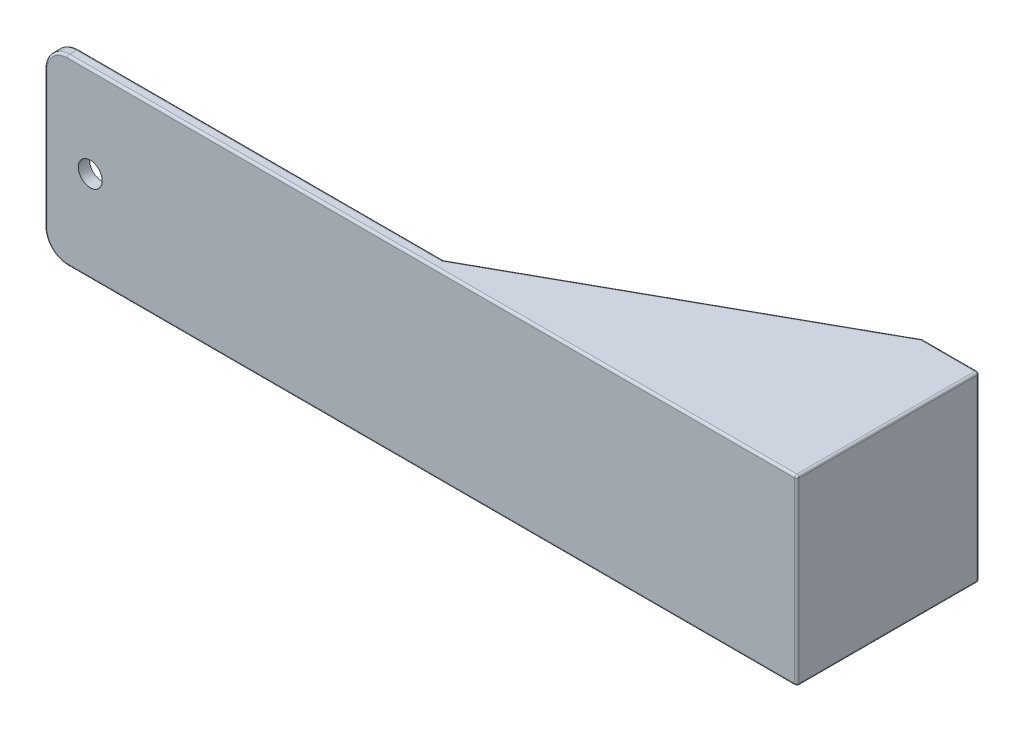
SolidWorks part; units mm, degrees
ref_plane "前视基准面" through (0, 0, 0) normal (0, 0, 1) x (1, 0, 0)
ref_plane "上视基准面" through (0, 0, 0) normal (0, 1, 0) x (1, 0, 0)
ref_plane "右视基准面" through (0, 0, 0) normal (1, 0, 0) x (0, 0, -1)
sketch "草图1" plane through (0, 0, 0) normal (0, 0, 1) x (1, 0, 0)
  line L1 (165, -40) -> (-165, -40)
  line L2 (165, -40) -> (165, 40)
  line L3 (165, 40) -> (-165, 40)
  line L4 (-165, -40) -> (-165, 40)
  line L5 (165, -40) -> (-165, 40) construction
  line L6 (165, 40) -> (-165, -40) construction
  point P0 (0, 0)
  dimension "D1" = 80
  dimension "D2" = 330
extrude "凸台-拉伸1" add sketch "草图1" along normal blind 5
sketch "草图2" plane through (0, 0, 5) normal (0, 0, 1) x (1, 0, 0)
  line L0 (-165, 40) -> (-165, -40) construction
  circle A0 centre (-145, 0) radius 5.25
  dimension "D1" = 10.5
  dimension "D2" = 20
extrude "切除-拉伸1" cut sketch "草图2" against normal blind 5
sketch "草图3" plane through (0, 0, 5) normal (0, 0, 1) x (1, 0, 0)
  circle A0 centre (-45, 0) radius 4
  dimension "D2" = 8
extrude "切除-拉伸2" cut sketch "草图3" against normal blind 10
fillet "圆角1" radius 10 2 edges at (-165, -40, 2.5) (-165, 40, 2.5)
sketch "草图13" plane through (0, 0, 5) normal (0, 0, 1) x (1, 0, 0)
  circle A0 centre (-45, 0) radius 6.9694
extrude "凸台-拉伸5" add sketch "草图13" against normal blind 5
sketch "草图14" plane through (0, -40, 0) normal (0, -1, 0) x (1, 0, 0)
  line L1 (165, 0) -> (160, 0)
  line L2 (165, 0) -> (165, -75)
  line L3 (165, -75) -> (160, -75)
  line L4 (160, 0) -> (160, -75)
  dimension "D1" = 5
  dimension "D2" = 75
extrude "凸台-拉伸6" add sketch "草图14" against normal up to surface (80 mm away) up to face at (5, 40, 2.5)
sketch "草图15" plane through (0, -40, 0) normal (0, -1, 0) x (1, 0, 0)
  line L1 (160, -75) -> (140, -75)
  line L2 (160, -75) -> (160, -70)
  line L3 (160, -70) -> (140, -70)
  line L4 (140, -75) -> (140, -70)
  dimension "D1" = 5
  dimension "D2" = 20
extrude "凸台-拉伸7" add sketch "草图15" against normal up to surface (80 mm away) up to face at (56.6667, 40, -23.3333)
sketch "草图16" plane through (0, -40, 0) normal (0, -1, 0) x (1, 0, 0)
  line L0 (5, 5) -> (5, 0)
  line L1 (-155, 5) -> (165, 5) construction
  line L2 (-155, 0) -> (160, 0) construction
  line L3 (5, 0) -> (140, -75)
  line L4 (140, -75) -> (165, -75)
  line L5 (165, -75) -> (165, 5)
  line L6 (165, 5) -> (5, 5)
  dimension "D1" = 160
extrude "凸台-拉伸8" add sketch "草图16" against normal blind 5
mirror "镜向1" about plane through (0, 0, 0) normal (0, 1, 0) of "凸台-拉伸8"
sketch "草图17" plane through (0, 0, -75) normal (0, 0, -1) x (-1, 0, 0)
  line L0 (-165, 40) -> (-165, -40) construction
  line L1 (-165, 0) -> (-114.5, 0) construction
  circle A0 centre (-152, -15) radius 3
  circle A1 centre (-152, 15) radius 3
  dimension "D1" = 6
  dimension "D3" = 30
  dimension "D2" = 13
extrude "切除-拉伸5" cut sketch "草图17" against normal blind 5
fillet "圆角2" radius 1 20 edges at (-162.0711, 37.0711, 5) (-165, 0, 5) (-162.0711, -37.0711, 5) (-162.0711, 37.0711, 0) (-165, 0, 0) (-162.0711, -37.0711, 0) (5, 40, 5) (-75, 40, 0) (72.5, 40, -37.5) (72.5, 35, -37.5) (152.5, 40, -75) (165, 0, -75) (165, 0, 5) (165, 40, -35) (5, -40, 5) (165, -40, -35) (152.5, -40, -75) (72.5, -40, -37.5) (72.5, -35, -37.5) (-75, -40, 0)
